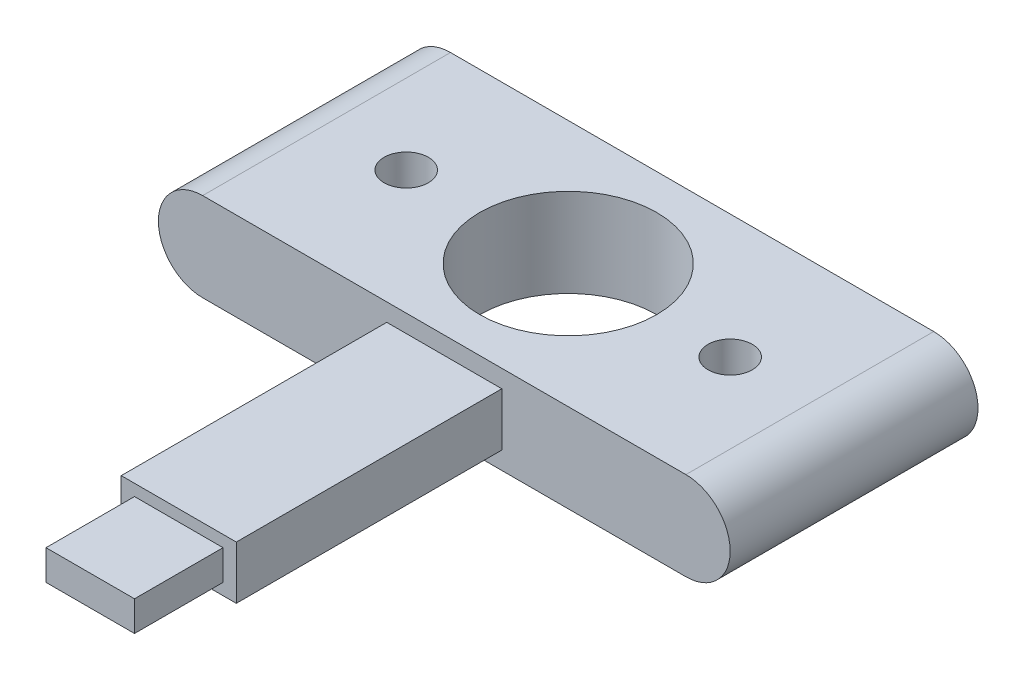
SolidWorks part; units mm, degrees
material "AISI 1045 Steel, cold drawn"
ref_plane "Front Plane" through (0, 0, 0) normal (0, 0, 1) x (1, 0, 0)
ref_plane "Top Plane" through (0, 0, 0) normal (0, 1, 0) x (1, 0, 0)
ref_plane "Right Plane" through (0, 0, 0) normal (1, 0, 0) x (0, 0, -1)
sketch "Sketch1" plane through (0, 0, 0) normal (0, 0, 1) x (1, 0, 0)
  line L0 (0, 6.35) -> (82.042, 6.35) construction
  line L1 (0, 0) -> (82.042, 0)
  line L2 (0, 0) -> (0, 12.7)
  line L3 (0, 12.7) -> (82.042, 12.7)
  line L4 (82.042, 0) -> (82.042, 12.7)
  line L5 (41.021, 6.35) -> (41.021, 12.7) construction
  arc A0 (75.692, 12.7) -> (75.692, 0) centre (75.692, 6.35) cw
  arc A1 (6.35, 12.7) -> (6.35, 0) centre (6.35, 6.35) ccw
  dimension "D1" = 12.7
  dimension "D2" = 82.042
extrude "Boss-Extrude1" add sketch "Sketch1" along normal blind 35.56 contours L3 A1 L1 A0
sketch "Sketch2" plane through (0, 12.7, 0) normal (0, 1, 0) x (1, 0, 0)
  line L0 (6.35, -35.56) -> (75.692, -35.56) construction
  line L1 (32.766, -35.56) -> (49.276, -35.56)
  line L2 (32.766, -35.56) -> (32.766, -73.66)
  line L3 (32.766, -73.66) -> (49.276, -73.66)
  line L4 (49.276, -35.56) -> (49.276, -73.66)
  line L5 (41.021, 0) -> (41.021, -73.66) construction
  line L6 (6.35, 0) -> (75.692, 0) construction
  dimension "D1" = 16.51
  dimension "D2" = 38.1
extrude "Boss-Extrude2" add sketch "Sketch2" against normal up to surface (12.7 mm away) up to face at (41.021, 0, 17.78)
sketch "Sketch3" plane through (32.766, 0, 0) normal (-1, 0, 0) x (0, 0, 1)
  line L0 (35.56, 6.35) -> (80.1985, 6.35) construction
  line L1 (35.56, 0) -> (35.56, 12.7) construction
  line L2 (73.66, 0) -> (73.66, 12.7) construction
  line L3 (35.56, 12.7) -> (73.66, 12.7)
  line L4 (35.56, 12.7) -> (35.56, 10.16)
  line L5 (35.56, 10.16) -> (73.66, 10.16)
  line L6 (73.66, 12.7) -> (73.66, 10.16)
  line L7 (73.66, 0) -> (73.66, 2.54)
  line L8 (35.56, 2.54) -> (73.66, 2.54)
  line L9 (35.56, 0) -> (35.56, 2.54)
  line L10 (35.56, 0) -> (73.66, 0)
  dimension "D1" = 2.54
extrude "Cut-Extrude1" cut sketch "Sketch3" against normal through all
sketch "Sketch4" plane through (0, 0, 73.66) normal (0, 0, 1) x (1, 0, 0)
  line L0 (32.766, 2.54) -> (49.276, 10.16) construction
  line L1 (34.671, 4.191) -> (47.371, 4.191)
  line L2 (34.671, 4.191) -> (34.671, 8.509)
  line L3 (34.671, 8.509) -> (47.371, 8.509)
  line L4 (47.371, 4.191) -> (47.371, 8.509)
  line L5 (34.671, 4.191) -> (47.371, 8.509) construction
  line L6 (34.671, 8.509) -> (47.371, 4.191) construction
  point P0 (41.021, 6.35)
  dimension "D1" = 4.318
  dimension "D2" = 12.7
extrude "Boss-Extrude3" add sketch "Sketch4" along normal blind 12.7
sketch "Sketch5" plane through (0, 12.7, 0) normal (0, 1, 0) x (1, 0, 0)
  line L0 (41.021, -17.78) -> (41.021, 0) construction
  line L1 (6.35, 0) -> (75.692, 0) construction
  line L2 (41.021, -17.78) -> (41.021, -35.56) construction
  line L3 (6.35, -35.56) -> (75.692, -35.56) construction
  circle A0 centre (41.021, -17.78) radius 12.7
  dimension "D1" = 25.4
  dimension "D2" = 17.78
extrude "Cut-Extrude2" cut sketch "Sketch5" against normal through all
sketch "Sketch6" plane through (0, 12.7, 0) normal (0, 1, 0) x (1, 0, 0)
  line L0 (6.35, -17.78) -> (75.692, -17.78) construction
  line L1 (6.35, -35.56) -> (6.35, 0) construction
  line L2 (75.692, -35.56) -> (75.692, 0) construction
  line L3 (41.021, -35.56) -> (41.021, 0) construction
  line L4 (6.35, -35.56) -> (75.692, -35.56) construction
  line L5 (6.35, 0) -> (75.692, 0) construction
  line L6 (82.042, -35.56) -> (82.042, 0) construction
  circle A0 centre (64.262, -17.78) radius 3.175
  circle A1 centre (17.78, -17.78) radius 3.175
  dimension "D1" = 6.35
  dimension "D2" = 17.78
extrude "Cut-Extrude3" cut sketch "Sketch6" against normal blind 5.08
